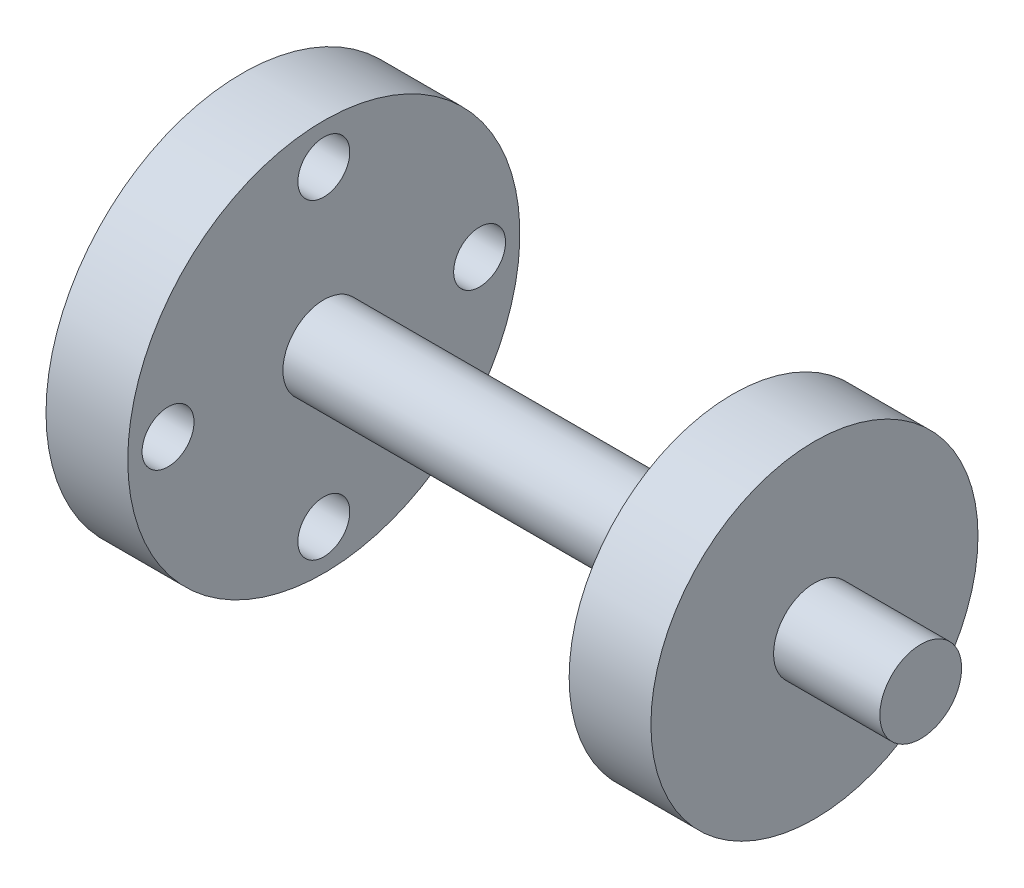
SolidWorks part; units mm, degrees
ref_plane "Front Plane" through (0, 0, 0) normal (0, 0, 1) x (1, 0, 0)
ref_plane "Top Plane" through (0, 0, 0) normal (0, 1, 0) x (1, 0, 0)
ref_plane "Right Plane" through (0, 0, 0) normal (1, 0, 0) x (0, 0, -1)
sketch "Sketch1" plane through (0, 0, 0) normal (0, 0, 1) x (1, 0, 0)
  line L0 (83, 5) -> (70, 5)
  line L1 (70, 5) -> (70, 20)
  line L2 (70, 20) -> (60, 20)
  line L3 (60, 20) -> (60, 5)
  line L4 (60, 5) -> (10, 5)
  line L5 (10, 5) -> (10, 23.975)
  line L6 (10, 23.975) -> (0, 23.975)
  line L7 (0, 23.975) -> (0, 0)
  line L8 (83, 5) -> (83, 0)
  line L9 (0, 0) -> (83, 0) construction
  line L10 (0, 0) -> (83, 0)
  point P2 (0, 0)
  point P3 (0, 0)
  point P12 (0, 0)
  point P13 (0, 0)
  point P14 (0, 0)
  dimension "D1" = 23.975
  dimension "7" = 10
  dimension "D2" = 10
  dimension "D3" = 13
  dimension "D4" = 15
  dimension "D5" = 50
  dimension "D6" = 5
revolve "Revolve1" add sketch "Sketch1" angle 360 about L9
sketch "Sketch3" plane through (0, 0, 0) normal (-1, 0, 0) x (0, 0, 1)
  circle A0 centre (0, 19.05) radius 3.175
  circle A1 centre (19.05, 0) radius 3.175
  circle A2 centre (0, -19.05) radius 3.175
  circle A3 centre (-19.05, 0) radius 3.175
  dimension "D1" = 6.35
  dimension "D2" = 19.05
  dimension "D3" = 4
extrude "Cut-Extrude1" cut sketch "Sketch3" against normal blind 10
